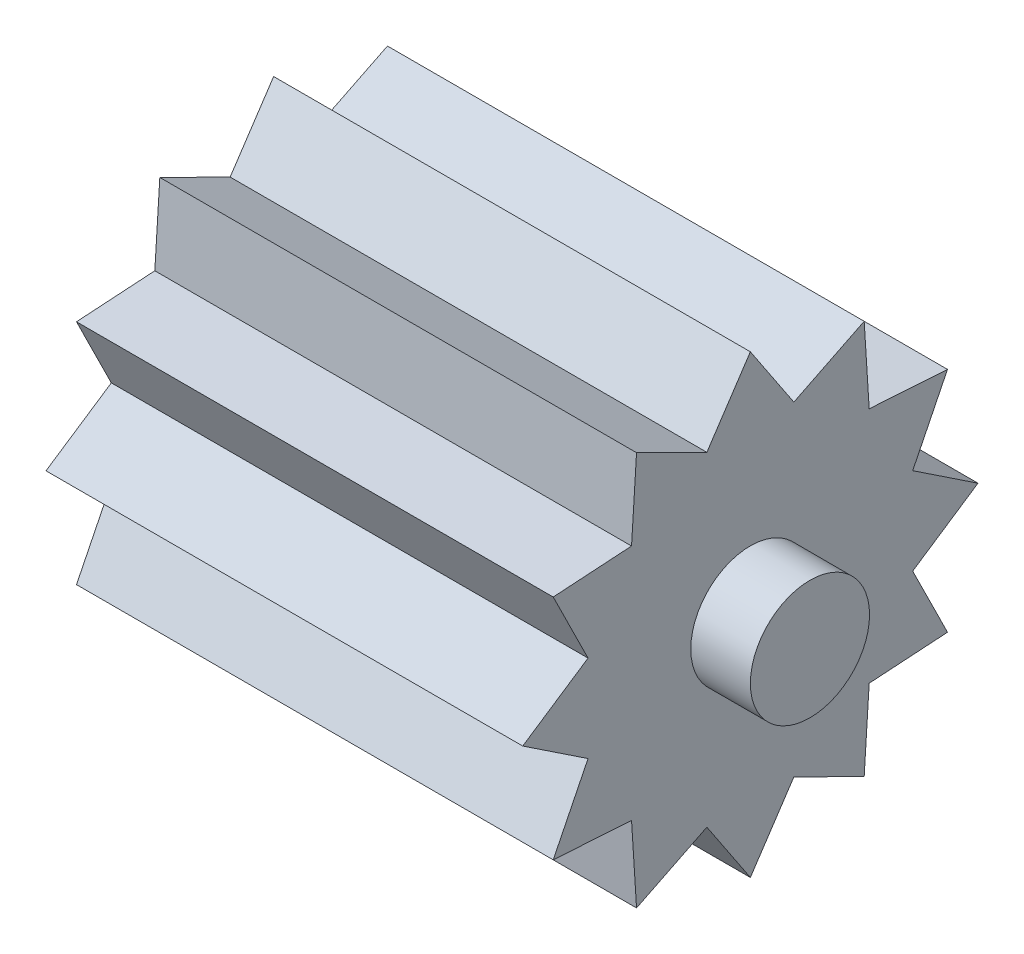
SolidWorks part; units mm, degrees
ref_plane "Front Plane" through (0, 0, 0) normal (0, 0, 1) x (1, 0, 0)
ref_plane "Top Plane" through (0, 0, 0) normal (0, 1, 0) x (1, 0, 0)
ref_plane "Right Plane" through (0, 0, 0) normal (1, 0, 0) x (0, 0, -1)
sketch "Sketch1" plane through (0, 0, 0) normal (1, 0, 0) x (0, 0, -1)
  line L0 (0, 0) -> (0, 9.55) construction
  line L1 (0, 0) -> (2.4717, 9.2246) construction
  line L2 (0, 9.55) -> (1.8247, 6.8098)
  line L3 (0, 9.55) -> (-1.8247, 6.8098)
  line L4 (4.775, 8.2705) -> (1.8247, 6.8098)
  line L5 (4.775, 8.2705) -> (4.9851, 4.9851)
  line L6 (8.2705, 4.775) -> (4.9851, 4.9851)
  line L7 (8.2705, 4.775) -> (6.8098, 1.8247)
  line L8 (9.55, 0) -> (6.8098, 1.8247)
  line L9 (9.55, 0) -> (6.8098, -1.8247)
  line L10 (8.2705, -4.775) -> (6.8098, -1.8247)
  line L11 (8.2705, -4.775) -> (4.9851, -4.9851)
  line L12 (4.775, -8.2705) -> (4.9851, -4.9851)
  line L13 (4.775, -8.2705) -> (1.8247, -6.8098)
  line L14 (0, -9.55) -> (1.8247, -6.8098)
  line L15 (0, -9.55) -> (-1.8247, -6.8098)
  line L16 (-4.775, -8.2705) -> (-1.8247, -6.8098)
  line L17 (-4.775, -8.2705) -> (-4.9851, -4.9851)
  line L18 (-8.2705, -4.775) -> (-4.9851, -4.9851)
  line L19 (-8.2705, -4.775) -> (-6.8098, -1.8247)
  line L20 (-9.55, 0) -> (-6.8098, -1.8247)
  line L21 (-9.55, 0) -> (-6.8098, 1.8247)
  line L22 (-8.2705, 4.775) -> (-6.8098, 1.8247)
  line L23 (-8.2705, 4.775) -> (-4.9851, 4.9851)
  line L24 (-4.775, 8.2705) -> (-4.9851, 4.9851)
  line L25 (-4.775, 8.2705) -> (-1.8247, 6.8098)
  point P1 (0, 0)
  point P43 (0, 0)
  dimension "D1" = 19.1
  dimension "D3" = 15
  dimension "D4" = 12
extrude "Boss-Extrude1" add sketch "Sketch1" against normal blind 10
sketch "Sketch4" plane through (0, 0, 0) normal (1, 0, 0) x (0, 0, -1)
  circle A0 centre (0, 0) radius 2.5
  dimension "D1" = 5
extrude "Boss-Extrude3" add sketch "Sketch4" along normal blind 2.5
mirror "Mirror1" about plane through (-10, 0, 0) normal (-1, 0, 0) of "Boss-Extrude1", "Boss-Extrude3"
